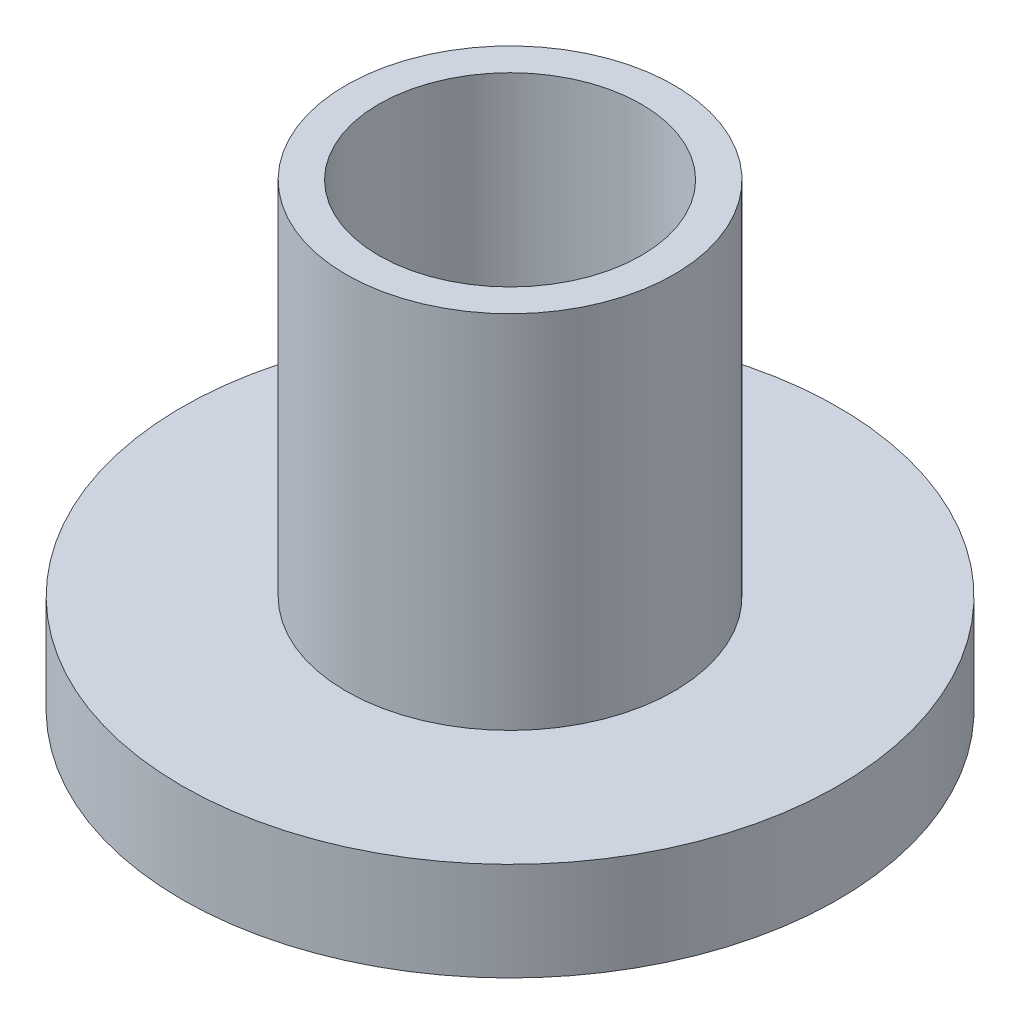
SolidWorks part; units mm, degrees
ref_plane "前视基准面" through (0, 0, 0) normal (0, 0, 1) x (1, 0, 0)
ref_plane "上视基准面" through (0, 0, 0) normal (0, 1, 0) x (1, 0, 0)
ref_plane "右视基准面" through (0, 0, 0) normal (1, 0, 0) x (0, 0, -1)
sketch "草图1" plane through (0, 0, 0) normal (0, 1, 0) x (1, 0, 0)
  circle A0 centre (0, 0) radius 5
  circle A1 centre (0, 0) radius 2
  dimension "D1" = 4
  dimension "D2" = 10
extrude "凸台-拉伸1" add sketch "草图1" along normal blind 1.5
sketch "草图2" plane through (0, 1.5, 0) normal (0, 1, 0) x (1, 0, 0)
  circle A0 centre (0, 0) radius 2 construction
  circle A1 centre (0, 0) radius 2
  circle A2 centre (0, 0) radius 2.5
  dimension "D1" = 5
extrude "凸台-拉伸2" add sketch "草图2" along normal blind 5.5
